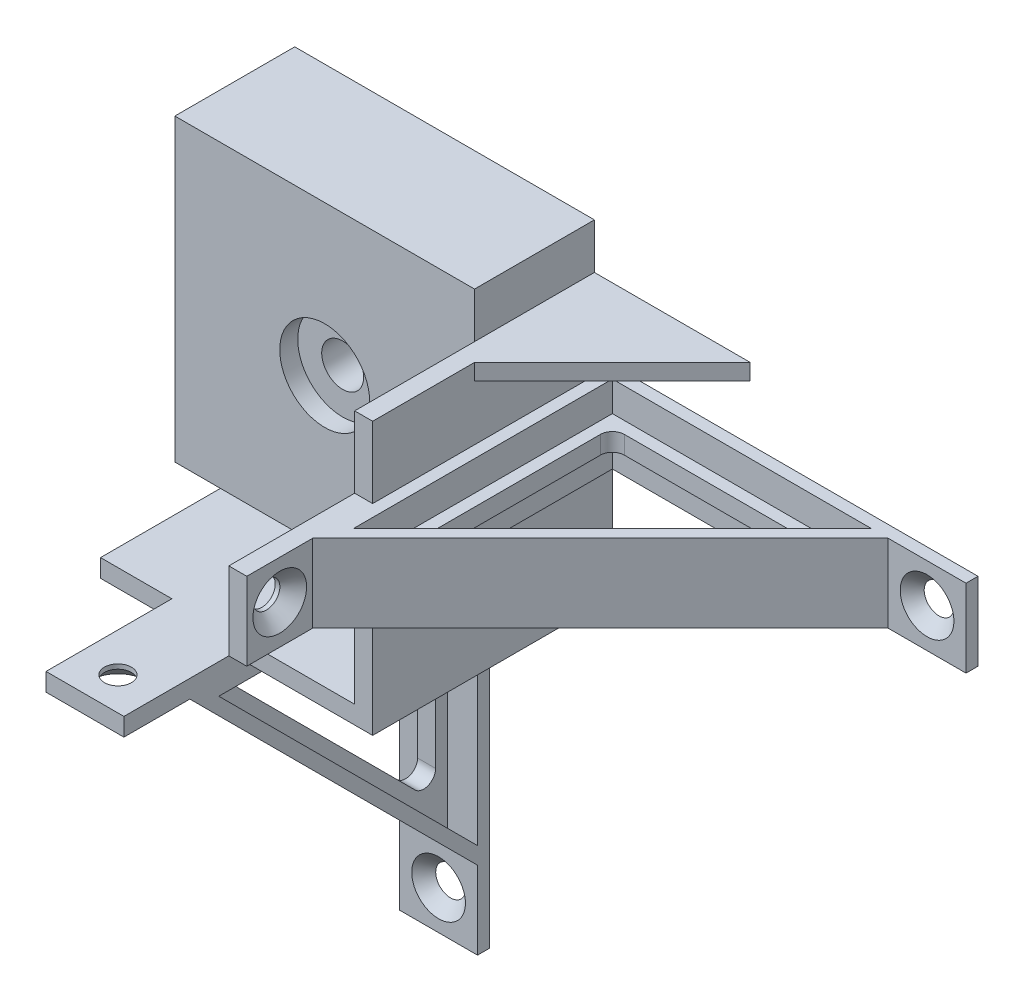
SolidWorks part; units mm, degrees
ref_plane "Alzado" through (0, 0, 0) normal (0, 0, 1) x (1, 0, 0)
ref_plane "Planta" through (0, 0, 0) normal (0, 1, 0) x (1, 0, 0)
ref_plane "Vista lateral" through (0, 0, 0) normal (1, 0, 0) x (0, 0, -1)
sketch "Croquis2" plane through (0, 0, 0) normal (0, 0, 1) x (1, 0, 0)
  line L1 (-25, -25) -> (25, -25)
  line L2 (-25, -25) -> (-25, 25)
  line L3 (-25, 25) -> (25, 25)
  line L4 (25, -25) -> (25, 25)
  line L5 (-25, -25) -> (25, 25) construction
  line L6 (-25, 25) -> (25, -25) construction
  circle A0 centre (0, 0) radius 3.5
  point P0 (0, 0)
  dimension "D3" = 7
  dimension "D1" = 50
  dimension "D2" = 50
extrude "Saliente-Extruir2" add sketch "Croquis2" along normal blind 20
sketch "Croquis3" plane through (0, 0, 20) normal (0, 0, 1) x (1, 0, 0)
  circle A0 centre (0, 0) radius 7.5
  dimension "D1" = 15
extrude "Cortar-Extruir1" cut sketch "Croquis3" against normal blind 3
sketch "Croquis4" plane through (0, 0, 0) normal (0, 0, -1) x (-1, 0, 0)
  line L0 (-25, -25) -> (-25, 17.4)
  line L1 (-25, -25) -> (-25, 25) construction
  line L2 (-25, -25) -> (17.4, -25)
  line L3 (25, -25) -> (-25, -25) construction
  line L4 (-25, 17.4) -> (-28, 17.4)
  line L5 (-28, 17.4) -> (-28, -28)
  line L6 (17.4, -25) -> (17.4, -28)
  line L7 (17.4, -28) -> (-28, -28)
  dimension "D1" = 7.6
  dimension "D2" = 7.6
  dimension "D3" = 3
  dimension "D4" = 3
extrude "Saliente-Extruir3" add sketch "Croquis4" against normal blind 40
sketch "Croquis5" plane through (0, 17.4, 0) normal (0, 1, 0) x (1, 0, 0)
  line L0 (25, 0) -> (51, 0)
  line L1 (25, 0) -> (25, -25)
  line L2 (25, -40) -> (25, -20) construction
  line L4 (25, -25) -> (26, -25)
  line L5 (26, -25) -> (51, 0)
  dimension "D1" = 26
  dimension "D2" = 25
  dimension "D3" = 1
extrude "Saliente-Extruir4" add sketch "Croquis5" against normal blind 2.65
sketch "Croquis6" plane through (0, 14.75, 0) normal (0, -1, 0) x (1, 0, 0)
  line L0 (38.4984, 12.5016) -> (37.7912, 11.7945) construction
  line L2 (44.9153, 4.6704) -> (30.6671, 18.9186)
  line L3 (44.9153, 4.6704) -> (40.5666, 0.3217)
  line L4 (40.5666, 0.3217) -> (26.3184, 14.5699)
  line L5 (26.3184, 14.5699) -> (30.6671, 18.9186)
  line L6 (51, 0) -> (25.9967, 25.0033) construction
  line L7 (28, 23) -> (51, 0) construction
  point P6 (37.7912, 11.7945)
  point P13 (38.4984, 12.5016)
  dimension "D1" = 1
  dimension "D2" = 20.15
  dimension "D3" = 6.15
  dimension "D4" = 35.36
extrude "Cortar-Extruir2" cut sketch "Croquis6" against normal blind 2 and the other way blind 3
ref_plane "Plano1" through (0, 0, 0) normal (0.7071, 0.7071, 0) x (0.7071, -0.7071, 0)
mirror "Simetría2" about plane through (0, 0, 0) normal (0.7071, 0.7071, 0) of "Cortar-Extruir2", "Saliente-Extruir4"
sketch "Croquis10" plane through (0, -28, 0) normal (0, -1, 0) x (1, 0, 0)
  line L0 (28, 0) -> (78, 0)
  line L1 (28, 0) -> (28, 40)
  line L2 (28, 50) -> (76, 2)
  line L3 (30, 45.1716) -> (73.1716, 2)
  line L4 (30, 2) -> (73.1716, 2)
  line L5 (30, 2) -> (30, 45.1716)
  line L6 (76, 2) -> (89, 2)
  line L7 (89, 2) -> (89, 0)
  line L8 (89, 0) -> (78, 0)
  line L9 (28, 40) -> (25, 40)
  line L10 (28, 50) -> (78, 0) construction
  line L11 (25, 40) -> (25, 61)
  line L12 (25, 61) -> (28, 61)
  line L13 (28, 61) -> (28, 50)
  line L15 (28, 0) -> (28, 50) construction
  dimension "D1" = 2
  dimension "D2" = 11
  dimension "D3" = 11
extrude "Saliente-Extruir5" add sketch "Croquis10" against normal blind 13 from offset 20.5 offset against normal yes
sketch "Croquis11" plane through (0, -7.5, 0) normal (0, -1, 0) x (1, 0, 0)
  line L3 (32, 40.3431) -> (32, 4)
  line L4 (32, 4) -> (68.3431, 4)
  line L5 (68.3431, 4) -> (32, 40.3431)
  line L6 (30, 45.1716) -> (30, 2)
  line L7 (73.1716, 2) -> (30, 45.1716)
  line L8 (30, 2) -> (73.1716, 2)
  line L9 (30, 45.1716) -> (30, 2)
  line L10 (73.1716, 2) -> (30, 45.1716)
  line L11 (30, 2) -> (73.1716, 2)
  dimension "D1" = 0
  dimension "D2" = 2
extrude "Saliente-Extruir6" add sketch "Croquis11" against normal blind 3 from offset 5 offset against normal yes
fillet "Redondeo1" radius 2 3 edges at (32, -1, 40.3431) (68.3431, -1, 4) (32, -1, 4)
sketch "Croquis12" plane through (0, 0, 2) normal (0, 0, 1) x (1, 0, 0)
  line L0 (89, 5.5) -> (89, -7.5) construction
  line L1 (89, -7.5) -> (76, -7.5) construction
  circle A0 centre (82.5, -1) radius 2
  point P6 (89, -1)
  point P10 (82.5, -7.5)
  dimension "D1" = 4
extrude "Cortar-Extruir4" cut sketch "Croquis12" against normal up to vertex (2 mm away)
sketch "Croquis13" plane through (28, 0, 0) normal (1, 0, 0) x (0, 0, -1)
  line L0 (-61, 5.5) -> (-61, -7.5) construction
  line L1 (-50, -7.5) -> (-61, -7.5) construction
  circle A0 centre (-55.5, -1) radius 2
  point P6 (-61, -1)
  point P10 (-55.5, -7.5)
  dimension "D1" = 4
extrude "Cortar-Extruir5" cut sketch "Croquis13" against normal up to vertex (3 mm away)
hole_wizard "Refrentado para tornillo tapón con cabeza plana de clavija de M41" positions "Croquis14" profile "Croquis15" countersink size "M4" standard "Ansi Metric" end condition through all
sketch "Croquis14" plane through (28, 0, 0) normal (1, 0, 0) x (0, 0, -1)
  point P0 (-55.5, -1)
sketch "Croquis15" plane through (28, -1, 55.5) normal (0, 1, 0) x (0, 0, -1)
  line L0 (0, 0) -> (0, 53)
  line L1 (0, 53) -> (2.25, 53)
  line L2 (2.25, 53) -> (2.25, 2.23)
  line L3 (2.25, 2.23) -> (4.48, 0)
  line L5 (4.48, 0) -> (0, 0)
  line L6 (-2.25, 2.23) -> (-4.48, 0) construction
  line L11 (0, -6.35) -> (0, 107.95) construction
  dimension "Diámetro de taladro hasta el siguiente" = 4.5
  dimension "Profundidad de taladro hasta el siguiente" = 53
  dimension "Diámetro de avellanado cercano" = 8.96
  dimension "Ángulo de avellanado cercano" = 90
hole_wizard "Refrentado para tornillo tapón con cabeza plana de clavija de M42" positions "Croquis16" profile "Croquis17" countersink size "M4" standard "Ansi Metric" end condition through all
sketch "Croquis16" plane through (0, 0, 2) normal (0, 0, 1) x (1, 0, 0)
  point P0 (82.5, -1)
sketch "Croquis17" plane through (82.5, -1, 2) normal (1, 0, 0) x (0, -1, 0)
  line L0 (0, 0) -> (0, 2)
  line L1 (0, 2) -> (2.25, 2)
  line L2 (2.25, 2) -> (2.25, 2.23)
  line L3 (2.25, 2.23) -> (4.48, 0)
  line L5 (4.48, 0) -> (0, 0)
  line L6 (-2.25, 2.23) -> (-4.48, 0) construction
  line L11 (0, -6.35) -> (0, 107.95) construction
  dimension "Diámetro de taladro hasta el siguiente" = 4.5
  dimension "Profundidad de taladro hasta el siguiente" = 2
  dimension "Diámetro de avellanado cercano" = 8.96
  dimension "Ángulo de avellanado cercano" = 90
mirror "Simetría4" about plane through (0, 0, 0) normal (0.7071, 0.7071, 0) of "Saliente-Extruir6", "Redondeo1", "Cortar-Extruir4", "Cortar-Extruir5", "Refrentado para tornillo tapón con cabeza plana de clavija de M41", "Refrentado para tornillo tapón con cabeza plana de clavija de M42", "Saliente-Extruir5"
